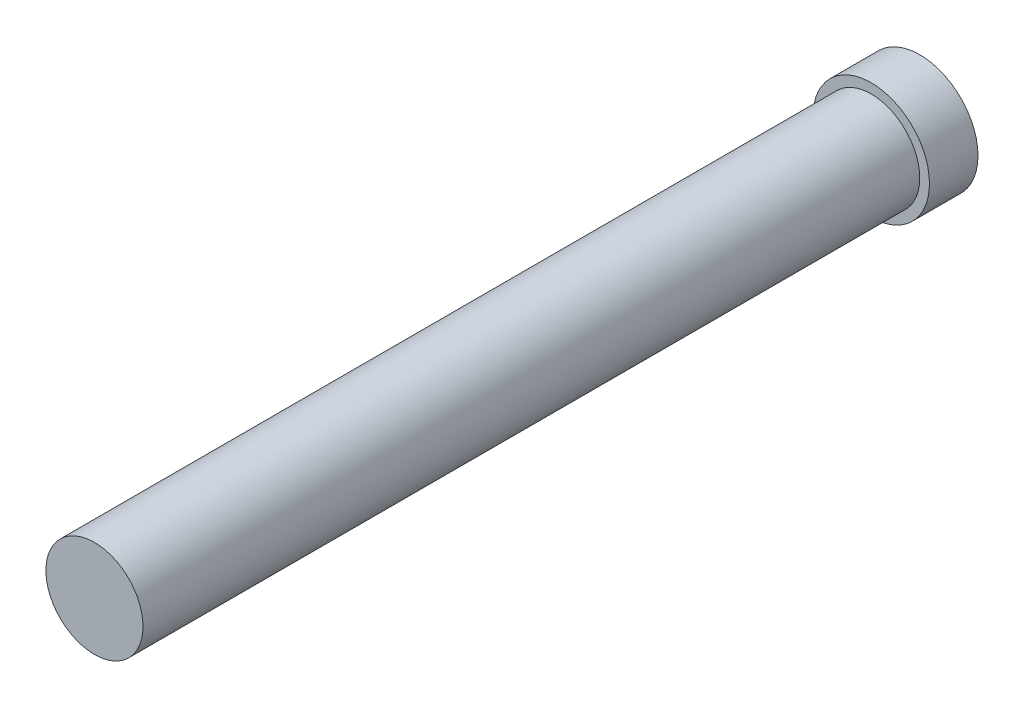
SolidWorks part; units mm, degrees
ref_plane "Front Plane" through (0, 0, 0) normal (0, 0, 1) x (1, 0, 0)
ref_plane "Top Plane" through (0, 0, 0) normal (0, 1, 0) x (1, 0, 0)
ref_plane "Right Plane" through (0, 0, 0) normal (1, 0, 0) x (0, 0, -1)
sketch "Sketch1" plane through (0, 0, 0) normal (0, 0, 1) x (1, 0, 0)
  circle A0 centre (0, 0) radius 7.62
  dimension "D1" = 15.24
extrude "Boss-Extrude1" add sketch "Sketch1" along normal blind 6.35
sketch "Sketch2" plane through (0, 0, 6.35) normal (0, 0, 1) x (1, 0, 0)
  circle A0 centre (0, 0) radius 6.35
  dimension "D1" = 12.7
extrude "Boss-Extrude2" add sketch "Sketch2" along normal blind 101.6
